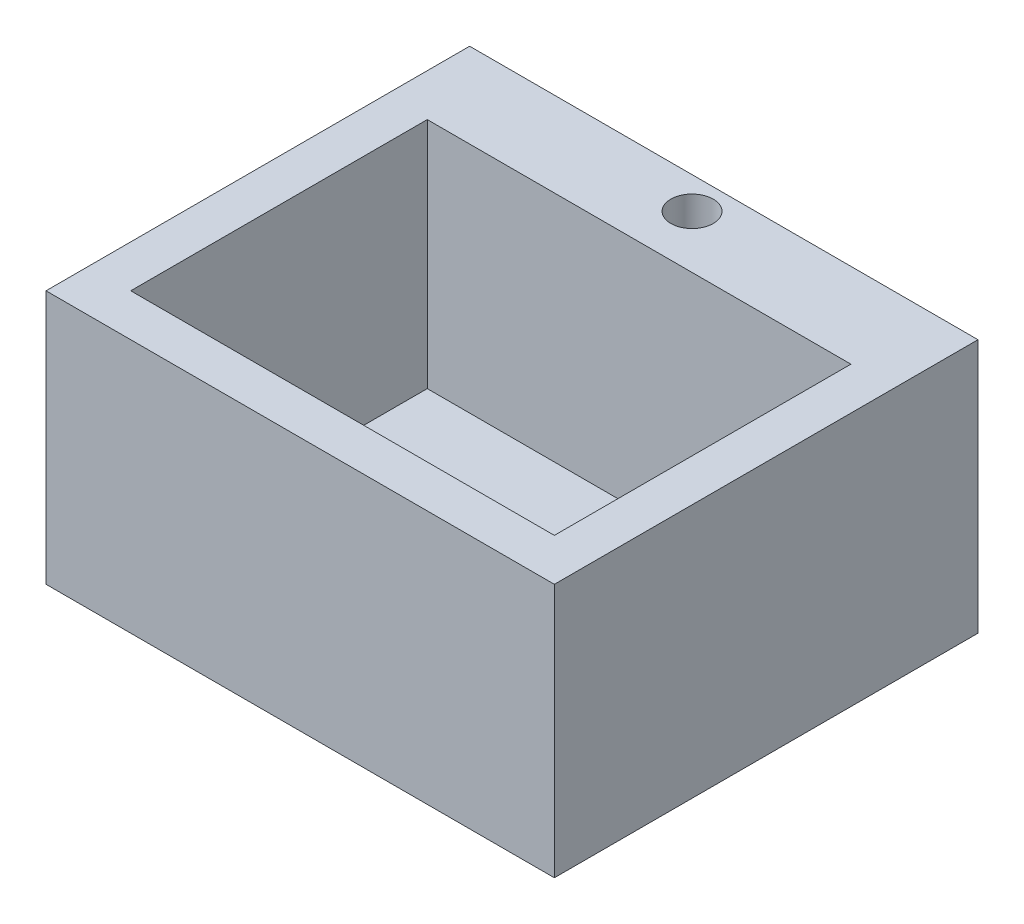
SolidWorks part; units mm, degrees
ref_plane "Front Plane" through (0, 0, 0) normal (0, 0, 1) x (1, 0, 0)
ref_plane "Top Plane" through (0, 0, 0) normal (0, 1, 0) x (1, 0, 0)
ref_plane "Right Plane" through (0, 0, 0) normal (1, 0, 0) x (0, 0, -1)
sketch "Sketch1" plane through (0, 0, 0) normal (0, 1, 0) x (1, 0, 0)
  line L1 (-130.0557, 64.7212) -> (174.7443, 64.7212)
  line L2 (-130.0557, 64.7212) -> (-130.0557, -189.2788)
  line L3 (-130.0557, -189.2788) -> (174.7443, -189.2788)
  line L4 (174.7443, 64.7212) -> (174.7443, -189.2788)
  circle A0 centre (22.3443, -81.3288) radius 19.05
  circle A1 centre (22.3443, 45.6712) radius 12.7
  dimension "D5" = 25.4
  dimension "D6" = 38.1
  dimension "D1" = 304.8
  dimension "D2" = 254
  dimension "D3" = 152.4
  dimension "D4" = 19.05
  dimension "D7" = 152.4
  dimension "D8" = 107.95
extrude "Boss-Extrude1" add sketch "Sketch1" against normal blind 152.4
sketch "Sketch2" plane through (0, 0, 0) normal (0, 1, 0) x (1, 0, 0)
  line L0 (-130.0557, 64.7212) -> (-130.0557, -189.2788) construction
  line L1 (-104.6557, 13.9212) -> (149.3443, 13.9212)
  line L2 (-104.6557, 13.9212) -> (-104.6557, -163.8788)
  line L3 (-104.6557, -163.8788) -> (149.3443, -163.8788)
  line L4 (149.3443, 13.9212) -> (149.3443, -163.8788)
  circle A1 centre (22.3443, -81.3288) radius 19.05 construction
  point P9 (22.3443, 13.9212)
  point P12 (41.1987, -163.8788)
  dimension "D4" = 177.8
  dimension "D5" = 82.55
  dimension "D1" = 25.4
  dimension "D2" = 25.4
  dimension "D3" = 25.4
extrude "Cut-Extrude1" cut sketch "Sketch2" against normal blind 139.7
